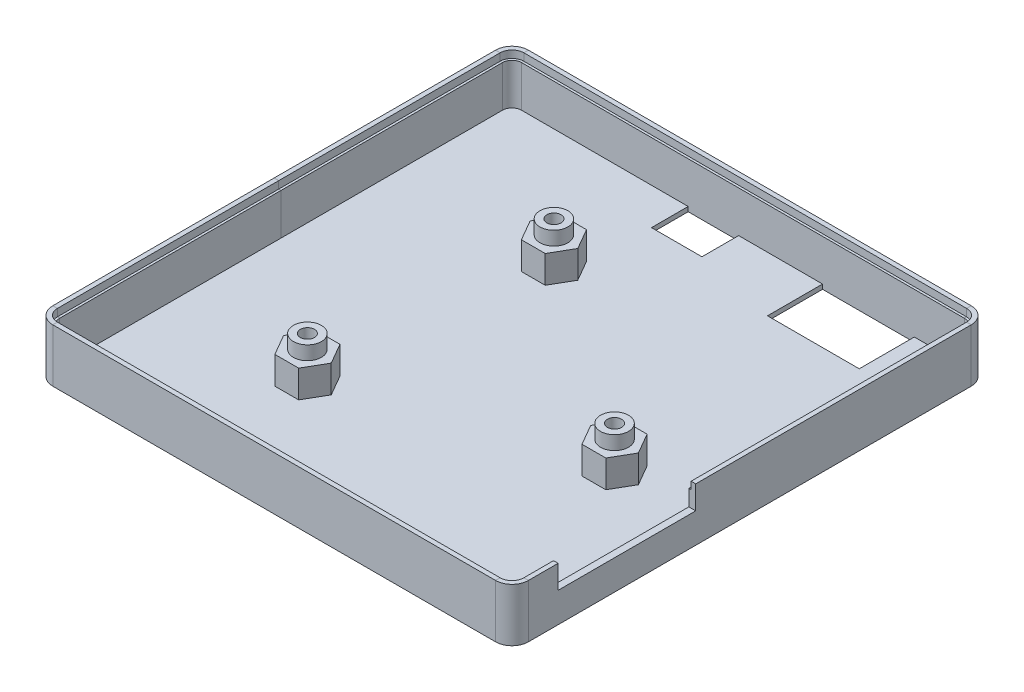
SolidWorks part; units mm, degrees
ref_plane "Front Plane" through (0, 0, 0) normal (0, 0, 1) x (1, 0, 0)
ref_plane "Top Plane" through (0, 0, 0) normal (0, 1, 0) x (1, 0, 0)
ref_plane "Right Plane" through (0, 0, 0) normal (1, 0, 0) x (0, 0, -1)
sketch "Sketch1" plane through (0, 0, 0) normal (0, 1, 0) x (1, 0, 0)
  line L1 (-48.26, -50.8) -> (48.26, -50.8)
  line L2 (-50.8, -48.26) -> (-50.8, 48.26)
  line L3 (-48.26, 50.8) -> (48.26, 50.8)
  line L4 (50.8, -48.26) -> (50.8, 48.26)
  line L5 (-50.8, -50.8) -> (50.8, 50.8) construction
  line L6 (-50.8, 50.8) -> (50.8, -50.8) construction
  arc A0 (48.26, 50.8) -> (50.8, 48.26) centre (48.26, 48.26) cw
  arc A1 (48.26, -50.8) -> (50.8, -48.26) centre (48.26, -48.26) ccw
  arc A2 (-48.26, -50.8) -> (-50.8, -48.26) centre (-48.26, -48.26) cw
  arc A3 (-50.8, 48.26) -> (-48.26, 50.8) centre (-48.26, 48.26) cw
  circle A4 centre (29.972, -7.62) radius 1.55
  circle A5 centre (-20.4724, -24.13) radius 1.55
  circle A6 centre (-15.24, 24.384) radius 1.55
  point P0 (0, 0)
  dimension "D1" = 2.54
  dimension "D6" = 3.1
  dimension "D9" = 24.384
  dimension "D2" = 101.6
  dimension "D3" = 101.6
  dimension "D4" = 29.972
  dimension "D5" = 7.62
  dimension "D7" = 20.4724
  dimension "D8" = 24.13
  dimension "D10" = 15.24
sketch "Sketch3" plane through (0, 0, 0) normal (0, 0, 1) x (1, 0, 0)
  line L0 (-50.85, 1.6) -> (-51.85, 1.6)
  line L1 (-51.85, 1.6) -> (-51.85, -10)
  line L2 (-50.85, 1.6) -> (-50.85, 0)
  line L4 (-50.35, 0) -> (-50.35, -10)
  line L5 (-51.85, -10) -> (-50.35, -10)
  line L7 (-50.85, 0) -> (-50.35, 0)
  point P5 (-50.8, 0)
  dimension "D1" = 1
  dimension "D2" = 1.6
  dimension "D3" = 0.5
  dimension "D4" = 10
  dimension "D5" = 0.05
sweep "Sweep1" add profiles "Sketch3" path "Sketch1"
sketch "Sketch5" plane through (0, -10, 0) normal (0, -1, 0) x (1, 0, 0)
  line L0 (-50.8, 48.26) -> (-50.8, -48.26) construction
  line L1 (-48.26, 50.8) -> (48.26, 50.8) construction
  line L2 (50.8, 48.26) -> (50.8, -48.26) construction
  line L3 (-48.26, -50.8) -> (48.26, -50.8) construction
  line L4 (-50.8, 48.26) -> (-50.8, -48.26)
  line L5 (-48.26, 50.8) -> (48.26, 50.8)
  line L6 (50.8, 48.26) -> (50.8, -48.26)
  line L7 (-48.26, -50.8) -> (48.26, -50.8)
  arc A0 (-48.26, 50.8) -> (-50.8, 48.26) centre (-48.26, 48.26) ccw construction
  arc A1 (50.8, 48.26) -> (48.26, 50.8) centre (48.26, 48.26) ccw construction
  arc A2 (48.26, -50.8) -> (50.8, -48.26) centre (48.26, -48.26) ccw construction
  arc A3 (-50.8, -48.26) -> (-48.26, -50.8) centre (-48.26, -48.26) ccw construction
  arc A4 (-48.26, 50.8) -> (-50.8, 48.26) centre (-48.26, 48.26) ccw
  arc A5 (50.8, 48.26) -> (48.26, 50.8) centre (48.26, 48.26) ccw
  arc A6 (48.26, -50.8) -> (50.8, -48.26) centre (48.26, -48.26) ccw
  arc A7 (-50.8, -48.26) -> (-48.26, -50.8) centre (-48.26, -48.26) ccw
  circle A8 centre (-15.24, -24.384) radius 1.55 construction
  circle A9 centre (29.972, 7.62) radius 1.55 construction
  circle A10 centre (-20.4724, 24.13) radius 1.55 construction
  circle A11 centre (-15.24, -24.384) radius 1.55
  circle A12 centre (29.972, 7.62) radius 1.55
  circle A13 centre (-20.4724, 24.13) radius 1.55
extrude "Boss-Extrude2" add sketch "Sketch5" against normal blind 1
sketch "Sketch6" plane through (0, 0, 0) normal (0, 1, 0) x (1, 0, 0)
  line L1 (-10.0438, 24.384) -> (-12.6419, 28.884)
  line L2 (-12.6419, 28.884) -> (-17.8381, 28.884)
  line L3 (-17.8381, 28.884) -> (-20.4362, 24.384)
  line L4 (-20.4362, 24.384) -> (-17.8381, 19.884)
  line L5 (-17.8381, 19.884) -> (-12.6419, 19.884)
  line L6 (-12.6419, 19.884) -> (-10.0438, 24.384)
  line L7 (35.1682, -7.62) -> (32.5701, -3.12)
  line L8 (32.5701, -3.12) -> (27.3739, -3.12)
  line L9 (27.3739, -3.12) -> (24.7758, -7.62)
  line L10 (24.7758, -7.62) -> (27.3739, -12.12)
  line L11 (27.3739, -12.12) -> (32.5701, -12.12)
  line L12 (32.5701, -12.12) -> (35.1682, -7.62)
  line L13 (-15.2762, -24.13) -> (-17.8743, -19.63)
  line L14 (-17.8743, -19.63) -> (-23.0705, -19.63)
  line L15 (-23.0705, -19.63) -> (-25.6686, -24.13)
  line L16 (-25.6686, -24.13) -> (-23.0705, -28.63)
  line L17 (-23.0705, -28.63) -> (-17.8743, -28.63)
  line L18 (-17.8743, -28.63) -> (-15.2762, -24.13)
  circle A3 centre (-15.24, 24.384) radius 1.55 construction
  circle A4 centre (29.972, -7.62) radius 1.55 construction
  circle A5 centre (-20.4724, -24.13) radius 1.55 construction
  circle A6 centre (-15.24, 24.384) radius 1.55
  circle A7 centre (29.972, -7.62) radius 1.55
  circle A8 centre (-20.4724, -24.13) radius 1.55
  circle A9 centre (-15.24, 24.384) radius 4.5 construction
  circle A10 centre (29.972, -7.62) radius 4.5 construction
  circle A11 centre (-20.4724, -24.13) radius 4.5 construction
  dimension "D1" = 9
extrude "Boss-Extrude3" add sketch "Sketch6" against normal up to surface (6 mm away) from offset 3 up to face at (-5.5944, -9, 0) offset against normal yes
sketch "Sketch7" plane through (0, -3, 0) normal (0, -1, 0) x (1, 0, 0)
  line L1 (-17.2392, 24.13) -> (-18.8558, 26.93)
  line L2 (-18.8558, 26.93) -> (-22.089, 26.93)
  line L3 (-22.089, 26.93) -> (-23.7056, 24.13)
  line L4 (-23.7056, 24.13) -> (-22.089, 21.33)
  line L5 (-22.089, 21.33) -> (-18.8558, 21.33)
  line L6 (-18.8558, 21.33) -> (-17.2392, 24.13)
  line L7 (33.2052, 7.62) -> (31.5886, 10.42)
  line L8 (31.5886, 10.42) -> (28.3554, 10.42)
  line L9 (28.3554, 10.42) -> (26.7388, 7.62)
  line L10 (26.7388, 7.62) -> (28.3554, 4.82)
  line L11 (28.3554, 4.82) -> (31.5886, 4.82)
  line L12 (31.5886, 4.82) -> (33.2052, 7.62)
  line L13 (-12.0068, -24.384) -> (-13.6234, -21.584)
  line L14 (-13.6234, -21.584) -> (-16.8566, -21.584)
  line L15 (-16.8566, -21.584) -> (-18.4732, -24.384)
  line L16 (-18.4732, -24.384) -> (-16.8566, -27.184)
  line L17 (-16.8566, -27.184) -> (-13.6234, -27.184)
  line L18 (-13.6234, -27.184) -> (-12.0068, -24.384)
  circle A0 centre (-20.4724, 24.13) radius 2.8 construction
  circle A1 centre (29.972, 7.62) radius 2.8 construction
  circle A2 centre (-15.24, -24.384) radius 2.8 construction
  dimension "D1" = 5.6
sketch "Sketch11" plane through (0, -3, 0) normal (0, 1, 0) x (1, 0, 0)
  circle A0 centre (-15.24, 24.384) radius 1.55 construction
  circle A1 centre (-20.4724, -24.13) radius 1.55 construction
  circle A2 centre (29.972, -7.62) radius 1.55 construction
  circle A3 centre (-15.24, 24.384) radius 1.55
  circle A4 centre (-20.4724, -24.13) radius 1.55
  circle A5 centre (29.972, -7.62) radius 1.55
  circle A6 centre (-15.24, 24.384) radius 3.05
  circle A7 centre (-20.4724, -24.13) radius 3.05
  circle A8 centre (29.972, -7.62) radius 3.05
  dimension "D1" = 1.5
extrude "Boss-Extrude4" add sketch "Sketch11" along normal up to surface (3 mm away) up to plane "Top Plane"
extrude "Cut-Extrude1" cut sketch "Sketch7" along normal through all from offset 2
sketch "Sketch8" plane through (0, -9, 0) normal (0, 1, 0) x (1, 0, 0)
  line L1 (-11.9408, 42.35) -> (-0.9408, 42.35)
  line L2 (-11.9408, 42.35) -> (-11.9408, 50.35)
  line L3 (-11.9408, 50.35) -> (-0.9408, 50.35)
  line L4 (-0.9408, 42.35) -> (-0.9408, 50.35)
  line L5 (-11.9408, 42.35) -> (-0.9408, 50.35) construction
  line L6 (-11.9408, 50.35) -> (-0.9408, 42.35) construction
  line L7 (50.35, 48.26) -> (50.35, -48.26) construction
  line L9 (50.35, -41.35) -> (50.35, -48.26)
  line L10 (25.8, -50.35) -> (48.26, -50.35)
  line L11 (25.8, -50.35) -> (25.8, -41.35)
  line L12 (25.8, -41.35) -> (50.35, -41.35)
  line L13 (50.8, -48.26) -> (50.8, 48.26) construction
  line L15 (17.35, 50.35) -> (37.35, 50.35)
  line L16 (17.35, 50.35) -> (17.35, 38.35)
  line L17 (17.35, 38.35) -> (37.35, 38.35)
  line L18 (37.35, 50.35) -> (37.35, 38.35)
  line L19 (-48.26, -50.35) -> (48.26, -50.35) construction
  line L20 (48.26, 50.35) -> (-48.26, 50.35) construction
  arc A1 (48.26, -50.35) -> (50.35, -48.26) centre (48.26, -48.26) ccw
  arc A3 (48.26, -50.35) -> (50.35, -48.26) centre (48.26, -48.26) ccw construction
  point P0 (-6.4408, 46.35)
  dimension "D1" = 11
  dimension "D2" = 25
  dimension "D3" = 9
  dimension "D4" = 8
  dimension "D5" = 6.4408
  dimension "D6" = 20
  dimension "D7" = 13
  dimension "D8" = 12
extrude "Cut-Extrude2" cut sketch "Sketch8" against normal through all
sketch "Sketch9" plane through (0, 0, 0) normal (0, 1, 0) x (1, 0, 0)
  line L0 (50.8, -48.26) -> (50.8, 48.26) construction
  line L1 (50.8, -41.8) -> (50.35, -41.8)
  line L2 (50.8, -41.8) -> (50.8, -11.8)
  line L3 (50.8, -11.8) -> (50.35, -11.8)
  line L4 (50.35, -41.8) -> (50.35, -11.8)
  line L5 (50.35, 48.26) -> (50.35, -41.35) construction
  line L6 (-48.26, -50.8) -> (48.26, -50.8) construction
  dimension "D1" = 9
  dimension "D2" = 39
extrude "Cut-Extrude3" cut sketch "Sketch9" against normal blind 3.5
sketch "Sketch10" plane through (51.85, 0, 0) normal (1, 0, 0) x (0, 0, -1)
  line L0 (-48.26, 1.6) -> (48.26, 1.6) construction
  line L1 (-11.8, -3.5) -> (-41.8, -3.5)
  line L2 (-11.8, -3.5) -> (-11.8, 1.6)
  line L3 (-11.8, 1.6) -> (-41.8, 1.6)
  line L4 (-41.8, -3.5) -> (-41.8, 1.6)
  line L5 (-41.8, -3.5) -> (-41.8, 0) construction
extrude "Cut-Extrude4" cut sketch "Sketch10" against normal up to next
